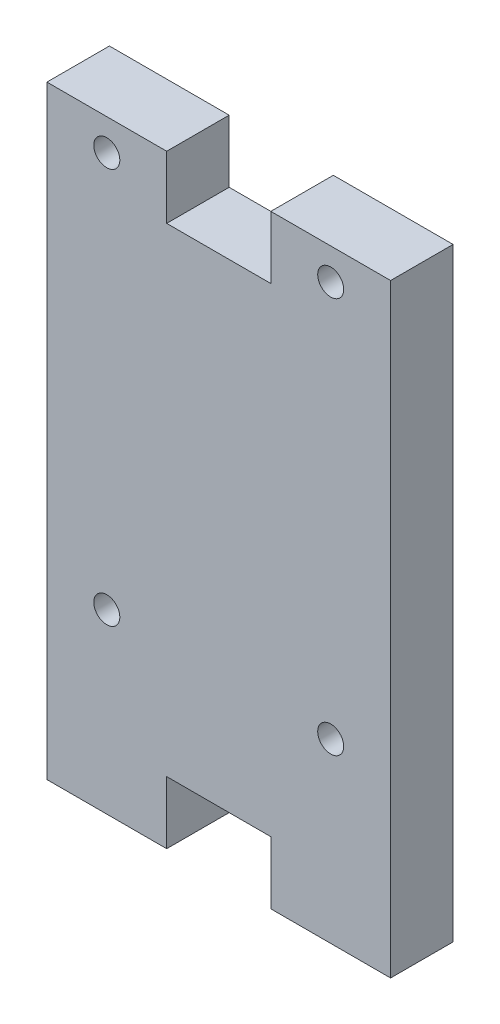
SolidWorks part; units mm, degrees
ref_plane "Plan de face" through (0, 0, 0) normal (0, 0, 1) x (1, 0, 0)
ref_plane "Plan de dessus" through (0, 0, 0) normal (0, 1, 0) x (1, 0, 0)
ref_plane "Plan de droite" through (0, 0, 0) normal (1, 0, 0) x (0, 0, -1)
sketch "Esquisse1" plane through (0, 0, 0) normal (0, 0, 1) x (1, 0, 0)
  line L0 (-16.5, 22) -> (-5, 22)
  line L1 (-5, 22) -> (-5, 16)
  line L2 (-16.5, 22) -> (-16.5, -36)
  line L3 (-16.5, -36) -> (-5, -36)
  line L4 (16.5, 22) -> (16.5, -36)
  line L5 (-5, 16) -> (5, 16)
  line L6 (5, 16) -> (5, 22)
  line L7 (5, 22) -> (16.5, 22)
  line L8 (-5, -36) -> (-5, -30)
  line L9 (-5, -30) -> (5, -30)
  line L10 (5, -30) -> (5, -36)
  line L11 (5, -36) -> (16.5, -36)
  line L12 (21.8917, 0) -> (-35.4168, 0) construction
  line L13 (0, 49.018) -> (0, -66.5613) construction
  dimension "D1" = 11.5
  dimension "D2" = 58
  dimension "D3" = 10
  dimension "D4" = 6
  dimension "D5" = 6
  dimension "D6" = 11.5
  dimension "D7" = 10
  dimension "D8" = 6
  dimension "D9" = 6
  dimension "D10" = 36
  dimension "D11" = 33
  dimension "D12" = 16.5
extrude "Boss.-Extru.1" add sketch "Esquisse1" along normal blind 6
sketch "Esquisse2" plane through (0, 0, 6) normal (0, 0, 1) x (1, 0, 0)
  line L0 (20.7527, 0) -> (-33.8611, 0) construction
  line L1 (-5, 22) -> (-16.5, 22) construction
  line L2 (16.5, 22) -> (5, 22) construction
  line L3 (5, 22) -> (5, 16) construction
  line L4 (-5, 16) -> (-5, 22) construction
  circle A0 centre (-10.75, 19) radius 1.25
  circle A1 centre (10.75, 19) radius 1.25
  circle A2 centre (10.75, -19) radius 1.25
  circle A3 centre (-10.75, -19) radius 1.25
  dimension "D2" = 2.5
  dimension "D4" = 2.5
  dimension "D1" = 3
  dimension "D3" = 3
  dimension "D5" = 5.75
  dimension "D6" = 5.75
extrude "Enlèv. mat.-Extru.1" cut sketch "Esquisse2" against normal blind 6
